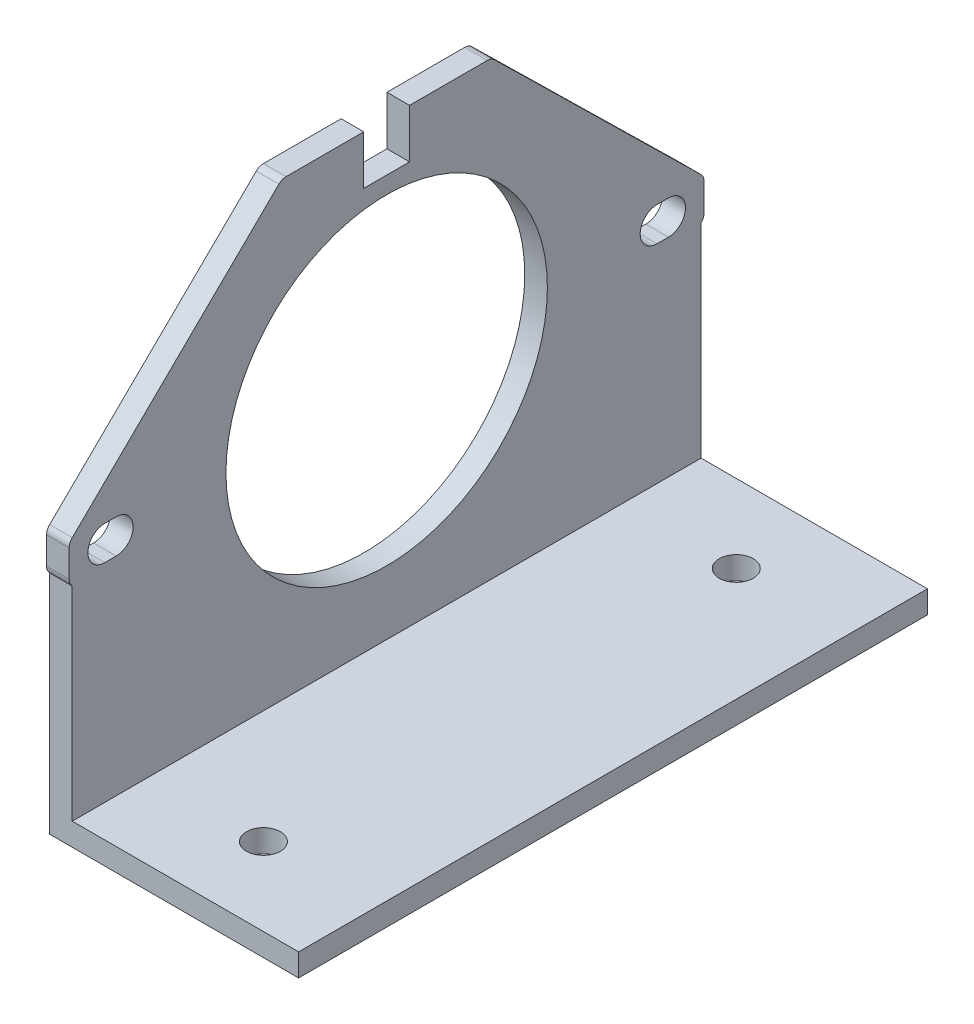
SolidWorks part; units mm, degrees
ref_plane "Front Plane" through (0, 0, 0) normal (0, 0, 1) x (1, 0, 0)
ref_plane "Top Plane" through (0, 0, 0) normal (0, 1, 0) x (1, 0, 0)
ref_plane "Right Plane" through (0, 0, 0) normal (1, 0, 0) x (0, 0, -1)
sketch "Sketch1" plane through (668.1397, 0, 0) normal (1, 0, 0) x (0, 0, -1)
  line L16 (-1313.7018, 878.517) -> (-1306.8355, 878.517)
  line L17 (-1306.8355, 878.517) -> (-1306.8355, 882.842)
  line L18 (-1306.8355, 882.842) -> (-1302.7855, 882.842)
  line L19 (-1302.7855, 882.842) -> (-1302.7855, 878.517)
  line L20 (-1302.7855, 878.517) -> (-1295.9192, 878.517)
  line L21 (-1295.2888, 878.7747) -> (-1277.0301, 896.6944)
  line L22 (-1276.7605, 897.3368) -> (-1276.7605, 899.7473)
  line L23 (-1277.0301, 900.3897) -> (-1295.2888, 918.3094)
  line L24 (-1295.9192, 918.567) -> (-1302.7855, 918.567)
  line L25 (-1302.7855, 918.567) -> (-1302.7855, 914.242)
  line L26 (-1302.7855, 914.242) -> (-1306.8355, 914.242)
  line L27 (-1306.8355, 914.242) -> (-1306.8355, 918.567)
  line L28 (-1306.8355, 918.567) -> (-1313.7018, 918.567)
  line L29 (-1314.3322, 918.3094) -> (-1332.5909, 900.3897)
  line L30 (-1332.8605, 899.7473) -> (-1332.8605, 897.3368)
  line L31 (-1332.5909, 896.6944) -> (-1314.3322, 878.7747)
  line L32 (-1313.7018, 878.517) -> (-1306.8355, 878.517)
  line L33 (-1306.8355, 878.517) -> (-1306.8355, 882.842)
  line L34 (-1306.8355, 882.842) -> (-1302.7855, 882.842)
  line L35 (-1302.7855, 882.842) -> (-1302.7855, 878.517)
  line L36 (-1302.7855, 878.517) -> (-1295.9192, 878.517)
  line L37 (-1295.2888, 878.7747) -> (-1277.0301, 896.6944)
  line L38 (-1276.7605, 897.3368) -> (-1276.7605, 899.7473)
  line L39 (-1277.0301, 900.3897) -> (-1295.2888, 918.3094)
  line L40 (-1295.9192, 918.567) -> (-1302.7855, 918.567)
  line L41 (-1302.7855, 918.567) -> (-1302.7855, 914.242)
  line L42 (-1302.7855, 914.242) -> (-1306.8355, 914.242)
  line L43 (-1306.8355, 914.242) -> (-1306.8355, 918.567)
  line L44 (-1306.8355, 918.567) -> (-1313.7018, 918.567)
  line L45 (-1314.3322, 918.3094) -> (-1332.5909, 900.3897)
  line L46 (-1332.8605, 899.7473) -> (-1332.8605, 897.3368)
  line L47 (-1332.5909, 896.6944) -> (-1314.3322, 878.7747)
  arc A0 (-1290.9022, 900.142) -> (-1314.2026, 908.9241) centre (-1304.8105, 898.542) ccw construction
  arc A1 (-1290.9022, 900.142) -> (-1314.2026, 908.9241) centre (-1304.8105, 898.542) ccw construction
  circle A2 centre (-1304.8105, 898.542) radius 14 construction
  circle A3 centre (-1304.8105, 898.542) radius 14.2
  arc A8 (-1295.9192, 878.517) -> (-1295.2888, 878.7747) centre (-1295.9192, 879.417) ccw
  arc A9 (-1277.0301, 896.6944) -> (-1276.7605, 897.3368) centre (-1277.6605, 897.3368) ccw
  arc A10 (-1276.7605, 899.7473) -> (-1277.0301, 900.3897) centre (-1277.6605, 899.7473) ccw
  arc A11 (-1295.2888, 918.3094) -> (-1295.9192, 918.567) centre (-1295.9192, 917.667) ccw
  arc A12 (-1313.7018, 918.567) -> (-1314.3322, 918.3094) centre (-1313.7018, 917.667) ccw
  arc A13 (-1332.5909, 900.3897) -> (-1332.8605, 899.7473) centre (-1331.9605, 899.7473) ccw
  arc A14 (-1332.8605, 897.3368) -> (-1332.5909, 896.6944) centre (-1331.9605, 897.3368) ccw
  arc A15 (-1314.3322, 878.7747) -> (-1313.7018, 878.517) centre (-1313.7018, 879.417) ccw
  arc A16 (-1295.9192, 878.517) -> (-1295.2888, 878.7747) centre (-1295.9192, 879.417) ccw
  arc A17 (-1277.0301, 896.6944) -> (-1276.7605, 897.3368) centre (-1277.6605, 897.3368) ccw
  arc A18 (-1276.7605, 899.7473) -> (-1277.0301, 900.3897) centre (-1277.6605, 899.7473) ccw
  arc A19 (-1295.2888, 918.3094) -> (-1295.9192, 918.567) centre (-1295.9192, 917.667) ccw
  arc A20 (-1313.7018, 918.567) -> (-1314.3322, 918.3094) centre (-1313.7018, 917.667) ccw
  arc A21 (-1332.5909, 900.3897) -> (-1332.8605, 899.7473) centre (-1331.9605, 899.7473) ccw
  arc A22 (-1332.8605, 897.3368) -> (-1332.5909, 896.6944) centre (-1331.9605, 897.3368) ccw
  arc A23 (-1314.3322, 878.7747) -> (-1313.7018, 878.517) centre (-1313.7018, 879.417) ccw
  line M25 (-1320.6605, 896.442) -> (-1325.0605, 896.442)
  line M26 (-1325.0605, 896.442) -> (-1325.0605, 900.642)
  line M27 (-1325.0605, 900.642) -> (-1320.6605, 900.642)
  line M28 (-1320.6605, 900.642) -> (-1320.6605, 896.442)
  line M29 (-1284.5605, 896.442) -> (-1288.9605, 896.442)
  line M30 (-1288.9605, 896.442) -> (-1288.9605, 900.642)
  line M31 (-1288.9605, 900.642) -> (-1284.5605, 900.642)
  line M32 (-1284.5605, 900.642) -> (-1284.5605, 896.442)
  line M35 (-1279.9105, 897.042) -> (-1280.9105, 897.042)
  arc M36 (-1280.9105, 897.042) -> (-1282.4105, 898.542) centre (-1280.9105, 898.542) cw
  arc M37 (-1282.4105, 898.542) -> (-1280.9105, 900.042) centre (-1280.9105, 898.542) cw
  line M38 (-1280.9105, 900.042) -> (-1279.9105, 900.042)
  arc M39 (-1279.9105, 900.042) -> (-1279.9105, 897.042) centre (-1279.9105, 898.542) cw
  arc M40 (-1328.7105, 900.042) -> (-1328.7105, 897.042) centre (-1328.7105, 898.542) cw
  line M41 (-1328.7105, 897.042) -> (-1329.7105, 897.042)
  arc M42 (-1329.7105, 897.042) -> (-1331.2105, 898.542) centre (-1329.7105, 898.542) cw
  arc M43 (-1331.2105, 898.542) -> (-1329.7105, 900.042) centre (-1329.7105, 898.542) cw
  line M44 (-1329.7105, 900.042) -> (-1328.7105, 900.042)
  line M45 (-1313.7018, 878.517) -> (-1306.8355, 878.517)
  line M46 (-1306.8355, 878.517) -> (-1306.8355, 882.842)
  line M47 (-1306.8355, 882.842) -> (-1302.7855, 882.842)
  line M48 (-1302.7855, 882.842) -> (-1302.7855, 878.517)
  line M49 (-1302.7855, 878.517) -> (-1295.9192, 878.517)
  arc M50 (-1295.9192, 878.517) -> (-1295.2888, 878.7747) centre (-1295.9192, 879.417) ccw
  line M51 (-1295.2888, 878.7747) -> (-1277.0301, 896.6944)
  arc M52 (-1277.0301, 896.6944) -> (-1276.7605, 897.3368) centre (-1277.6605, 897.3368) ccw
  line M53 (-1276.7605, 897.3368) -> (-1276.7605, 899.7473)
  arc M54 (-1276.7605, 899.7473) -> (-1277.0301, 900.3897) centre (-1277.6605, 899.7473) ccw
  line M55 (-1277.0301, 900.3897) -> (-1295.2888, 918.3094)
  arc M56 (-1295.2888, 918.3094) -> (-1295.9192, 918.567) centre (-1295.9192, 917.667) ccw
  line M57 (-1295.9192, 918.567) -> (-1302.7855, 918.567)
  line M58 (-1302.7855, 918.567) -> (-1302.7855, 914.242)
  line M59 (-1302.7855, 914.242) -> (-1306.8355, 914.242)
  line M60 (-1306.8355, 914.242) -> (-1306.8355, 918.567)
  line M61 (-1306.8355, 918.567) -> (-1313.7018, 918.567)
  arc M62 (-1313.7018, 918.567) -> (-1314.3322, 918.3094) centre (-1313.7018, 917.667) ccw
  line M63 (-1314.3322, 918.3094) -> (-1332.5909, 900.3897)
  arc M64 (-1332.5909, 900.3897) -> (-1332.8605, 899.7473) centre (-1331.9605, 899.7473) ccw
  line M65 (-1332.8605, 899.7473) -> (-1332.8605, 897.3368)
  arc M66 (-1332.8605, 897.3368) -> (-1332.5909, 896.6944) centre (-1331.9605, 897.3368) ccw
  line M67 (-1332.5909, 896.6944) -> (-1314.3322, 878.7747)
  arc M68 (-1314.3322, 878.7747) -> (-1313.7018, 878.517) centre (-1313.7018, 879.417) ccw
  dimension "D2" = 0.2
extrude "Boss-Extrude1" add sketch "Sketch1" along normal blind 2 contours A3 M68 M45 M46 M47 M48 M49 M50 M51 M52 M53 M54 M55 M56 M57 M58 M59 M60 M61 M62 M63 M64 M65 M66 M67 M44 M40 M41 M42 M43 M39 M35 M36 M37 M38 M32 M29 M30 M31 M28 M25 M26 M27 | M25 M28 M27 M26 | M29 M32 M31 M30
sketch "Sketch2" plane through (670.1397, 0, 0) normal (1, 0, 0) x (0, 0, -1)
  line L0 (-1332.5909, 896.6944) -> (-1332.5909, 876.6944)
  line L1 (-1332.5909, 876.6944) -> (-1277.0301, 876.6944)
  line L2 (-1277.0301, 876.6944) -> (-1277.0301, 896.6944)
  line L16 (-1313.7018, 878.517) -> (-1306.8355, 878.517)
  line L17 (-1306.8355, 878.517) -> (-1306.8355, 882.842)
  line L18 (-1306.8355, 882.842) -> (-1302.7855, 882.842)
  line L19 (-1302.7855, 882.842) -> (-1302.7855, 878.517)
  line L20 (-1302.7855, 878.517) -> (-1295.9192, 878.517)
  line L21 (-1295.2888, 878.7747) -> (-1277.0301, 896.6944)
  line L22 (-1276.7605, 897.3368) -> (-1276.7605, 899.7473)
  line L23 (-1277.0301, 900.3897) -> (-1295.2888, 918.3094)
  line L24 (-1295.9192, 918.567) -> (-1302.7855, 918.567)
  line L25 (-1302.7855, 918.567) -> (-1302.7855, 914.242)
  line L26 (-1302.7855, 914.242) -> (-1306.8355, 914.242)
  line L27 (-1306.8355, 914.242) -> (-1306.8355, 918.567)
  line L28 (-1306.8355, 918.567) -> (-1313.7018, 918.567)
  line L29 (-1314.3322, 918.3094) -> (-1332.5909, 900.3897)
  line L30 (-1332.8605, 899.7473) -> (-1332.8605, 897.3368)
  line L31 (-1332.5909, 896.6944) -> (-1314.3322, 878.7747)
  line L32 (-1313.7018, 878.517) -> (-1306.8355, 878.517)
  line L33 (-1306.8355, 878.517) -> (-1306.8355, 882.842)
  line L34 (-1306.8355, 882.842) -> (-1302.7855, 882.842)
  line L35 (-1302.7855, 882.842) -> (-1302.7855, 878.517)
  line L36 (-1302.7855, 878.517) -> (-1295.9192, 878.517)
  line L37 (-1295.2888, 878.7747) -> (-1277.0301, 896.6944)
  line L38 (-1276.7605, 897.3368) -> (-1276.7605, 899.7473)
  line L39 (-1277.0301, 900.3897) -> (-1295.2888, 918.3094)
  line L40 (-1295.9192, 918.567) -> (-1302.7855, 918.567)
  line L41 (-1302.7855, 918.567) -> (-1302.7855, 914.242)
  line L42 (-1302.7855, 914.242) -> (-1306.8355, 914.242)
  line L43 (-1306.8355, 914.242) -> (-1306.8355, 918.567)
  line L44 (-1306.8355, 918.567) -> (-1313.7018, 918.567)
  line L45 (-1314.3322, 918.3094) -> (-1332.5909, 900.3897)
  line L46 (-1332.8605, 899.7473) -> (-1332.8605, 897.3368)
  line L47 (-1332.5909, 896.6944) -> (-1314.3322, 878.7747)
  arc A8 (-1314.3322, 878.7747) -> (-1313.7018, 878.517) centre (-1313.7018, 879.417) ccw
  arc A9 (-1295.9192, 878.517) -> (-1295.2888, 878.7747) centre (-1295.9192, 879.417) ccw
  arc A10 (-1277.0301, 896.6944) -> (-1276.7605, 897.3368) centre (-1277.6605, 897.3368) ccw
  arc A11 (-1276.7605, 899.7473) -> (-1277.0301, 900.3897) centre (-1277.6605, 899.7473) ccw
  arc A12 (-1295.2888, 918.3094) -> (-1295.9192, 918.567) centre (-1295.9192, 917.667) ccw
  arc A13 (-1313.7018, 918.567) -> (-1314.3322, 918.3094) centre (-1313.7018, 917.667) ccw
  arc A14 (-1332.5909, 900.3897) -> (-1332.8605, 899.7473) centre (-1331.9605, 899.7473) ccw
  arc A15 (-1332.8605, 897.3368) -> (-1332.5909, 896.6944) centre (-1331.9605, 897.3368) ccw
  arc A16 (-1314.3322, 878.7747) -> (-1313.7018, 878.517) centre (-1313.7018, 879.417) ccw
  arc A17 (-1295.9192, 878.517) -> (-1295.2888, 878.7747) centre (-1295.9192, 879.417) ccw
  arc A18 (-1277.0301, 896.6944) -> (-1276.7605, 897.3368) centre (-1277.6605, 897.3368) ccw
  arc A19 (-1276.7605, 899.7473) -> (-1277.0301, 900.3897) centre (-1277.6605, 899.7473) ccw
  arc A20 (-1295.2888, 918.3094) -> (-1295.9192, 918.567) centre (-1295.9192, 917.667) ccw
  arc A21 (-1313.7018, 918.567) -> (-1314.3322, 918.3094) centre (-1313.7018, 917.667) ccw
  arc A22 (-1332.5909, 900.3897) -> (-1332.8605, 899.7473) centre (-1331.9605, 899.7473) ccw
  arc A23 (-1332.8605, 897.3368) -> (-1332.5909, 896.6944) centre (-1331.9605, 897.3368) ccw
  arc M29 (-1314.3322, 878.7747) -> (-1313.7018, 878.517) centre (-1313.7018, 879.417) ccw
  line M30 (-1313.7018, 878.517) -> (-1306.8355, 878.517)
  line M31 (-1306.8355, 878.517) -> (-1306.8355, 882.842)
  line M32 (-1306.8355, 882.842) -> (-1302.7855, 882.842)
  line M33 (-1302.7855, 882.842) -> (-1302.7855, 878.517)
  line M34 (-1302.7855, 878.517) -> (-1295.9192, 878.517)
  arc M35 (-1295.9192, 878.517) -> (-1295.2888, 878.7747) centre (-1295.9192, 879.417) ccw
  line M36 (-1295.2888, 878.7747) -> (-1277.0301, 896.6944)
  line M52 (-1332.5909, 896.6944) -> (-1314.3322, 878.7747)
  dimension "D2" = 20
  dimension "D1" = 0
extrude "Boss-Extrude2" add sketch "Sketch2" against normal up to surface (2 mm away) contours L1 L2 L0 M36 M35 M34 M33 M32 M31 M30 M29 M52 up to face at (668.1397, 898.542, 1290.6105)
sketch "Sketch3" plane through (670.1397, 0, 0) normal (1, 0, 0) x (0, 0, -1)
  line L1 (-1332.5909, 876.6944) -> (-1277.0301, 876.6944)
  line L2 (-1332.5909, 876.6944) -> (-1332.5909, 878.6944)
  line L3 (-1332.5909, 878.6944) -> (-1277.0301, 878.6944)
  line L4 (-1277.0301, 876.6944) -> (-1277.0301, 878.6944)
  line L12 (-1332.5909, 896.6944) -> (-1332.5909, 876.6944)
  line L13 (-1332.5909, 876.6944) -> (-1277.0301, 876.6944)
  line L14 (-1277.0301, 876.6944) -> (-1277.0301, 896.6944)
  line L15 (-1276.7605, 897.3368) -> (-1276.7605, 899.7473)
  line L16 (-1277.0301, 900.3897) -> (-1295.2888, 918.3094)
  line L17 (-1295.9192, 918.567) -> (-1302.7855, 918.567)
  line L18 (-1302.7855, 918.567) -> (-1302.7855, 914.242)
  line L19 (-1302.7855, 914.242) -> (-1306.8355, 914.242)
  line L20 (-1306.8355, 914.242) -> (-1306.8355, 918.567)
  line L21 (-1306.8355, 918.567) -> (-1313.7018, 918.567)
  line L22 (-1314.3322, 918.3094) -> (-1332.5909, 900.3897)
  line L23 (-1332.8605, 899.7473) -> (-1332.8605, 897.3368)
  line L24 (-1332.5909, 896.6944) -> (-1332.5909, 876.6944)
  line L25 (-1332.5909, 876.6944) -> (-1277.0301, 876.6944)
  line L26 (-1277.0301, 876.6944) -> (-1277.0301, 896.6944)
  line L27 (-1276.7605, 897.3368) -> (-1276.7605, 899.7473)
  line L28 (-1277.0301, 900.3897) -> (-1295.2888, 918.3094)
  line L29 (-1295.9192, 918.567) -> (-1302.7855, 918.567)
  line L30 (-1302.7855, 918.567) -> (-1302.7855, 914.242)
  line L31 (-1302.7855, 914.242) -> (-1306.8355, 914.242)
  line L32 (-1306.8355, 914.242) -> (-1306.8355, 918.567)
  line L33 (-1306.8355, 918.567) -> (-1313.7018, 918.567)
  line L34 (-1314.3322, 918.3094) -> (-1332.5909, 900.3897)
  line L35 (-1332.8605, 899.7473) -> (-1332.8605, 897.3368)
  arc A6 (-1332.8605, 897.3368) -> (-1332.5909, 896.6944) centre (-1331.9605, 897.3368) ccw
  arc A7 (-1277.0301, 896.6944) -> (-1276.7605, 897.3368) centre (-1277.6605, 897.3368) ccw
  arc A8 (-1276.7605, 899.7473) -> (-1277.0301, 900.3897) centre (-1277.6605, 899.7473) ccw
  arc A9 (-1295.2888, 918.3094) -> (-1295.9192, 918.567) centre (-1295.9192, 917.667) ccw
  arc A10 (-1313.7018, 918.567) -> (-1314.3322, 918.3094) centre (-1313.7018, 917.667) ccw
  arc A11 (-1332.5909, 900.3897) -> (-1332.8605, 899.7473) centre (-1331.9605, 899.7473) ccw
  arc A12 (-1332.8605, 897.3368) -> (-1332.5909, 896.6944) centre (-1331.9605, 897.3368) ccw
  arc A13 (-1277.0301, 896.6944) -> (-1276.7605, 897.3368) centre (-1277.6605, 897.3368) ccw
  arc A14 (-1276.7605, 899.7473) -> (-1277.0301, 900.3897) centre (-1277.6605, 899.7473) ccw
  arc A15 (-1295.2888, 918.3094) -> (-1295.9192, 918.567) centre (-1295.9192, 917.667) ccw
  arc A16 (-1313.7018, 918.567) -> (-1314.3322, 918.3094) centre (-1313.7018, 917.667) ccw
  arc A17 (-1332.5909, 900.3897) -> (-1332.8605, 899.7473) centre (-1331.9605, 899.7473) ccw
  line M22 (-1332.5909, 896.6944) -> (-1332.5909, 876.6944)
  line M23 (-1332.5909, 876.6944) -> (-1277.0301, 876.6944)
  line M24 (-1277.0301, 876.6944) -> (-1277.0301, 896.6944)
  dimension "D2" = 2
  dimension "D1" = 0
extrude "Boss-Extrude3" add sketch "Sketch3" along normal blind 20 contours L3 M22 M23 M24
sketch "Sketch4" plane through (0, 878.6944, 0) normal (0, 1, 0) x (1, 0, 0)
  line L0 (680.1397, -1277.0301) -> (680.1397, -1332.5909)
  line L1 (701.2397, -1290.8105) -> (668.2397, -1290.8105) construction
  line L2 (701.2397, -1290.8105) -> (668.2397, -1290.8105)
  line L3 (690.1397, -1277.0301) -> (690.1397, -1290.8105)
  line L4 (670.1397, -1277.0301) -> (670.1397, -1332.5909)
  line L5 (670.1397, -1332.5909) -> (690.1397, -1332.5909)
  line L6 (690.1397, -1332.5909) -> (690.1397, -1277.0301)
  line L7 (690.1397, -1277.0301) -> (670.1397, -1277.0301)
  line L8 (670.1397, -1277.0301) -> (670.1397, -1332.5909)
  line L9 (670.1397, -1332.5909) -> (690.1397, -1332.5909)
  line L10 (690.1397, -1332.5909) -> (690.1397, -1277.0301)
  line L11 (690.1397, -1277.0301) -> (670.1397, -1277.0301)
  line L12 (670.1397, -1304.8105) -> (690.1397, -1304.8105)
  circle A0 centre (680.1397, -1283.9203) radius 1.5
  circle A2 centre (680.1397, -1325.7007) radius 1.5
  point P10 (690.1397, -1283.9203)
  dimension "D2" = 3
  dimension "D1" = 0
extrude "Cut-Extrude1" cut sketch "Sketch4" against normal up to surface (2 mm away) contours L0 A0 | L0 A0 | A2 L0 | A2 L0 up to face at (679.1397, 876.6944, 1304.8105)
equation "\"T\"=2"
equation "\"D1@Boss-Extrude1\"=\"T\""
equation "\"C\"=0.2"
equation "\"D2@Sketch1\"=\"C\""
equation "\"H\"=34.6522"
equation "\"L\"=20"
equation "\"D1@Boss-Extrude3\"=\"L\""
equation "\"SCREWD\"=4.17471"
